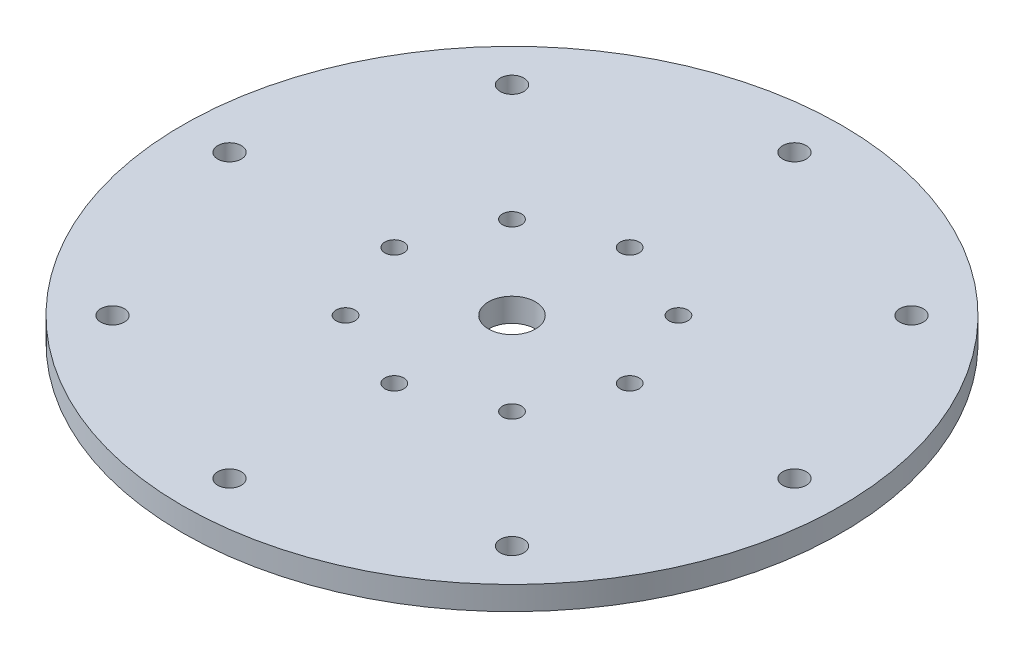
SolidWorks part; units mm, degrees
material "AISI 316 Stainless Steel Sheet (SS)"
ref_plane "Front Plane" through (0, 0, 0) normal (0, 0, 1) x (1, 0, 0)
ref_plane "Top Plane" through (0, 0, 0) normal (0, 1, 0) x (1, 0, 0)
ref_plane "Right Plane" through (0, 0, 0) normal (1, 0, 0) x (0, 0, -1)
sketch "Sketch1" plane through (0, 0, 0) normal (0, 1, 0) x (1, 0, 0)
  circle A0 centre (0, 0) radius 6.35
  circle A1 centre (0, 0) radius 88.9
  dimension "D1" = 12.7
  dimension "D2" = 177.8
extrude "Boss-Extrude1" add sketch "Sketch1" along normal blind 6.35
hole_wizard "CSK for #10 Flat Head Machine Screw (100)1" positions "3DSketch2" profile "Sketch3" countersink size "#10" standard "ANSI Inch" end condition through all
sketch3d "3DSketch2"
  line L0 (0, 0, 0) -> (31.75, 0, 0) construction
  point P9 (31.75, 0, 0)
  dimension "D1" = 31.75
sketch "Sketch3" plane through (31.75, 0, 0) normal (1, 0, 0) x (0, 0, -1)
  line L0 (0, 0) -> (0, 6.35)
  line L1 (0, 6.35) -> (2.5527, 6.35)
  line L2 (2.5527, 6.35) -> (2.5527, 1.9608)
  line L3 (2.5527, 1.9608) -> (4.8895, 0)
  line L5 (4.8895, 0) -> (0, 0)
  line L6 (-2.5527, 1.9608) -> (-4.8895, 0) construction
  line L11 (0, -6.35) -> (0, 107.95) construction
  dimension "Thru Hole Dia." = 5.1054
  dimension "Thru Hole Depth" = 6.35
  dimension "Near C'Sink Dia." = 9.779
  dimension "Near C'Sink Angle" = 100
hole_wizard "1/4 (0.25) Diameter Hole1" positions "Sketch4" profile "Sketch5" hole size "1/4" standard "ANSI Inch" end condition through all
sketch "Sketch4" plane through (0, 6.35, 0) normal (0, 1, 0) x (1, 0, 0)
  line L0 (88.9, 0) -> (76.2, 0) construction
  circle A0 centre (0, 0) radius 88.9 construction
  point P0 (76.2, 0)
  point P9 (75.4549, -11.4858)
  dimension "D1" = 12.7
sketch "Sketch5" plane through (76.2, 6.35, 0) normal (1, 0, 0) x (0, 0, 1)
  line L0 (0, 0) -> (0, 6.35)
  line L1 (0, 6.35) -> (3.175, 6.35)
  line L2 (3.175, 6.35) -> (3.175, 0)
  line L5 (3.175, 0) -> (0, 0)
  line L11 (0, -6.35) -> (0, 107.95) construction
  dimension "Thru Hole Dia." = 6.35
  dimension "Thru Hole Depth" = 6.35
pattern_circular "CirPattern1" count 8 over 360 about axis through (0, 0, 0) along (0, 1, 0) of "CSK for #10 Flat Head Machine Screw (100)1", "1/4 (0.25) Diameter Hole1"
